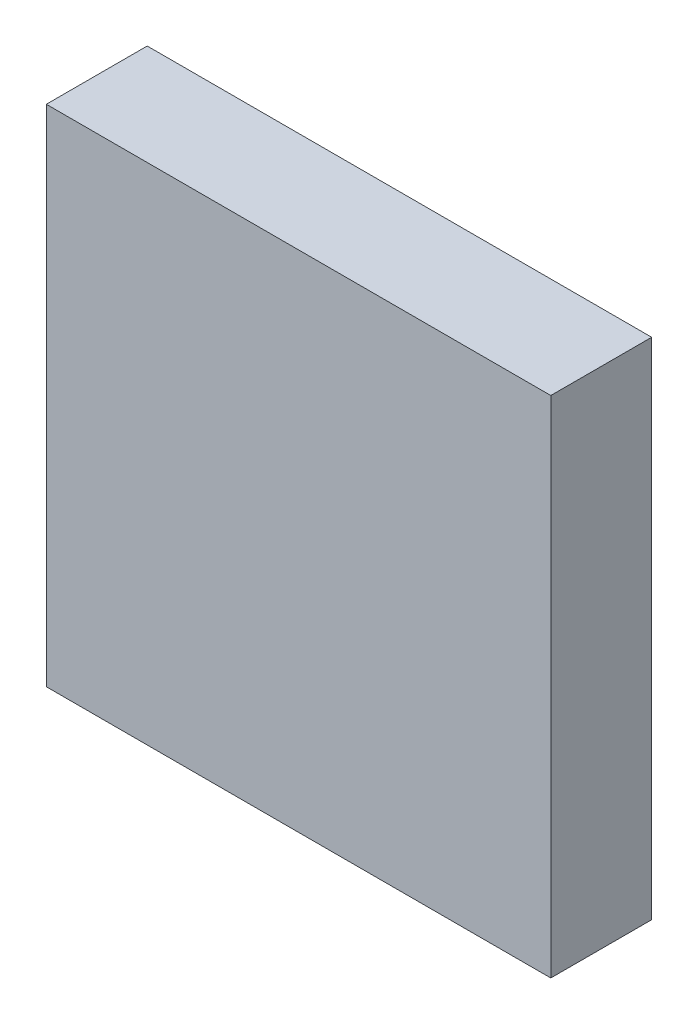
SolidWorks part; units mm, degrees
ref_plane "前视基准面" through (0, 0, 0) normal (0, 0, 1) x (1, 0, 0)
ref_plane "上视基准面" through (0, 0, 0) normal (0, 1, 0) x (1, 0, 0)
ref_plane "右视基准面" through (0, 0, 0) normal (1, 0, 0) x (0, 0, -1)
sketch "草图1" plane through (0, 0, 0) normal (0, 0, 1) x (1, 0, 0)
  line L0 (402.7887, 154.5864) -> (476.6299, 154.5864) construction
  line L1 (441.6175, 187.0122) -> (441.6175, 121.7564) construction
  line L2 (416.6175, 154.3843) -> (416.6175, 179.3843)
  line L3 (416.6175, 179.3843) -> (466.6175, 179.3843)
  line L4 (466.6175, 179.3843) -> (466.6175, 129.3843)
  line L5 (466.6175, 129.3843) -> (416.6175, 129.3843)
  line L6 (416.6175, 129.3843) -> (416.6175, 154.3843)
  dimension "D1" = 50
extrude "凸台-拉伸1" add sketch "草图1" along normal blind 10
